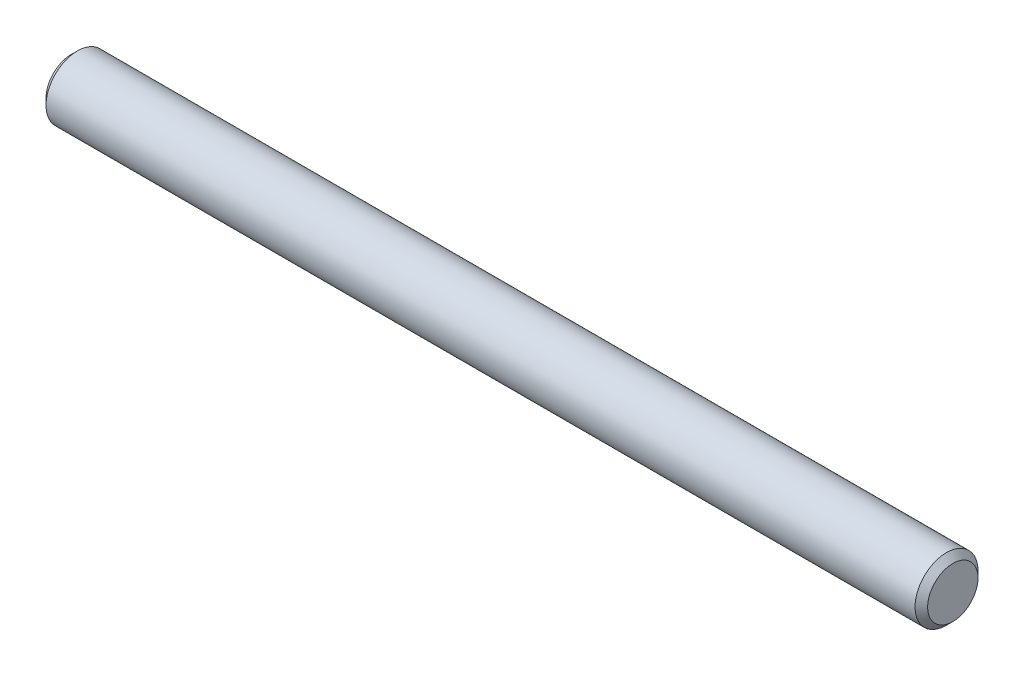
SolidWorks part; units mm, degrees
material "AISI 316 Annealed Stainless Steel Bar (SS)"
ref_plane "Front" through (0, 0, 0) normal (0, 0, 1) x (1, 0, 0)
ref_plane "Top" through (0, 0, 0) normal (0, 1, 0) x (1, 0, 0)
ref_plane "Right" through (0, 0, 0) normal (1, 0, 0) x (0, 0, -1)
sketch "Sketch1" plane through (0, 0, 0) normal (0, 0, 1) x (1, 0, 0)
  line L0 (-11.1125, 0) -> (11.1125, 0) construction
  line L1 (11.1125, 0.7937) -> (11.1125, -0.7937) construction
  line L2 (-11.1125, 0.7937) -> (-11.1125, -0.7937) construction
  dimension "Length" = 22.225
  dimension "Diameter" = 1.5875
sketch "Sketch2" plane through (0, 0, 0) normal (1, 0, 0) x (0, 0, -1)
  circle A0 centre (0, 0) radius 0.7937
extrude "Extrude1" add sketch "Sketch2" against normal up to vertex (11.1125 mm away) and the other way up to vertex (11.1125 mm away) up to point (-11.1125, 0.7937, 0) other way up to point (11.1125, 0.7937, 0)
chamfer "Chamfer1" distance 0.1588 angle 45 2 edges at (11.1125, 0, -0.7937) (-11.1125, 0, -0.7937)
equation "\"D1@Chamfer1\" = \"Diameter@Sketch1\"*.1"
